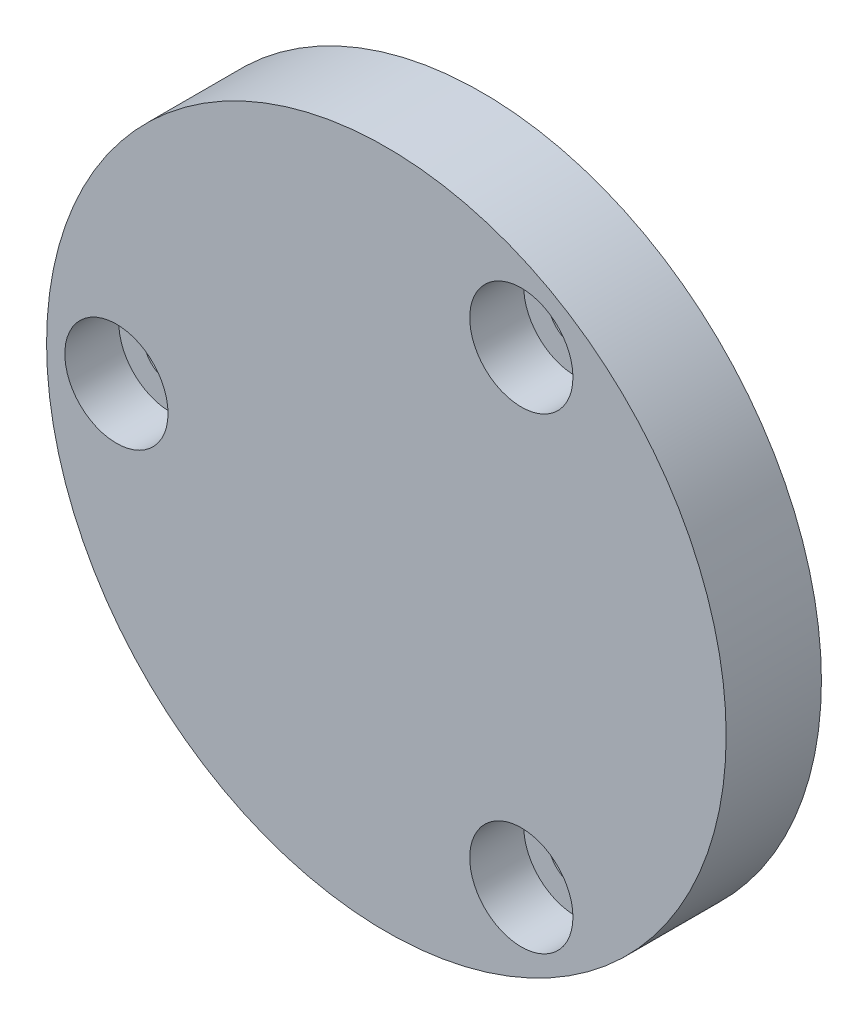
SolidWorks part; units mm, degrees
ref_plane "Plan de face" through (0, 0, 0) normal (0, 0, 1) x (1, 0, 0)
ref_plane "Plan de dessus" through (0, 0, 0) normal (0, 1, 0) x (1, 0, 0)
ref_plane "Plan de droite" through (0, 0, 0) normal (1, 0, 0) x (0, 0, -1)
sketch "Esquisse1" plane through (0, 0, 0) normal (0, 0, 1) x (1, 0, 0)
  circle A0 centre (0, 0) radius 21.4
  dimension "D1" = 42.8
extrude "Boss.-Extru.1" add sketch "Esquisse1" along normal blind 6
sketch "Esquisse2" plane through (0, 0, 0) normal (0, 0, -1) x (-1, 0, 0)
  circle A0 centre (0, 0) radius 12.5
  dimension "D1" = 25
extrude "Enlèv. mat.-Extru.1" cut sketch "Esquisse2" against normal blind 3
hole_wizard "Chambrage pour vis à tête hexagonale M31" positions "Esquisse3" profile "Esquisse4" counterbore size "M3" standard "ISO"
sketch "Esquisse3" plane through (0, 0, 6) normal (0, 0, 1) x (1, 0, 0)
  point P0 (-17, 0)
  point P8 (8.5, 14.7224)
  point P9 (8.5, -14.7224)
  dimension "D1" = 17
  dimension "D2" = 3
sketch "Esquisse4" plane through (-17, 0, 6) normal (1, 0, 0) x (0, -1, 0)
  line L0 (0, 0) -> (0, 9.0215)
  line L1 (0, 9.0215) -> (1.7, 8)
  line L2 (1.7, 8) -> (1.7, 3.4)
  line L3 (1.7, 3.4) -> (3.25, 3.4)
  line L4 (3.25, 3.4) -> (3.25, 0)
  line L5 (3.25, 0) -> (0, 0)
  line L10 (0, 9.0215) -> (-1.7, 8) construction
  line L11 (0, -6.35) -> (0, 107.95) construction
  dimension "Diamètre du perçage" = 3.4
  dimension "Profondeur du perçage" = 8
  dimension "Diamètre du chambrage" = 6.5
  dimension "Profondeur du chambrage" = 3.4
  dimension "Angle de pointe" = 118
